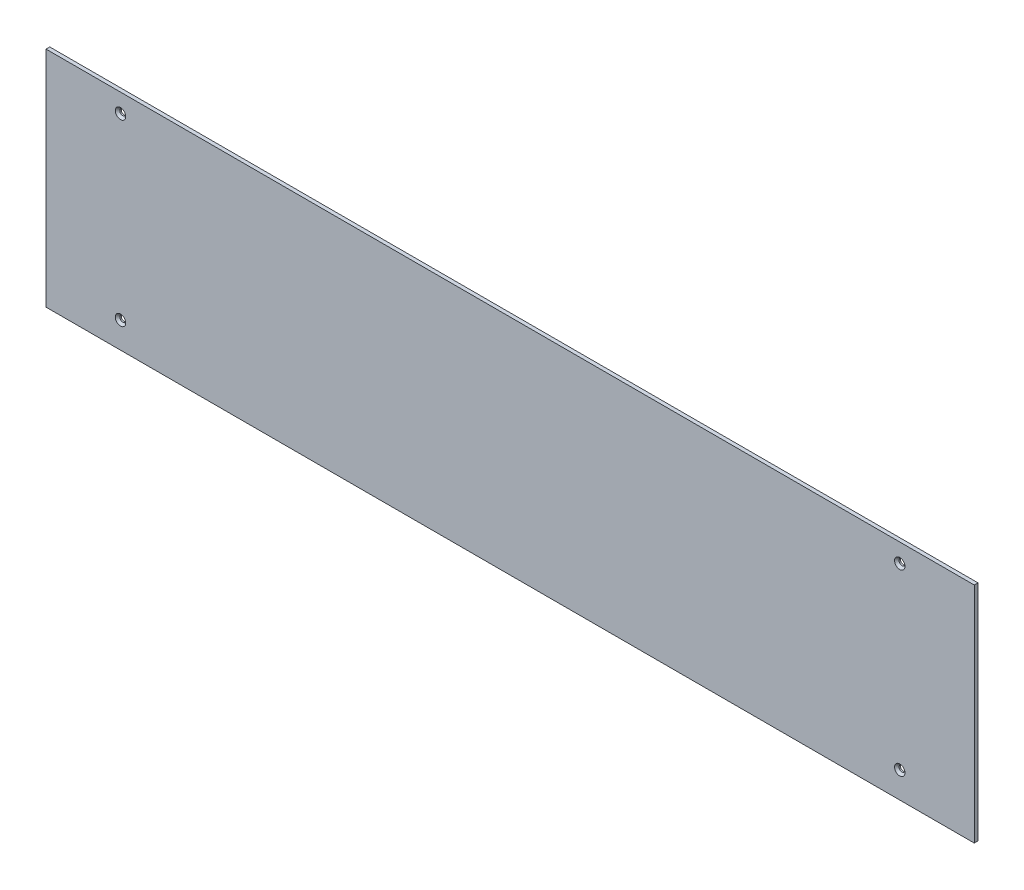
SolidWorks part; units mm, degrees
material "Glass"
ref_plane "Front Plane" through (0, 0, 0) normal (0, 0, 1) x (1, 0, 0)
ref_plane "Top Plane" through (0, 0, 0) normal (0, 1, 0) x (1, 0, 0)
ref_plane "Right Plane" through (0, 0, 0) normal (1, 0, 0) x (0, 0, -1)
sketch "Sketch1" plane through (0, 0, 0) normal (0, 0, 1) x (1, 0, 0)
  line L1 (-623, -150) -> (623, -150)
  line L2 (-623, -150) -> (-623, 150)
  line L3 (-623, 150) -> (623, 150)
  line L4 (623, -150) -> (623, 150)
  line L5 (-623, -150) -> (623, 150) construction
  line L6 (-623, 150) -> (623, -150) construction
  point P0 (0, 0)
  dimension "Largura" = 1246
  dimension "Altura" = 300
extrude "Boss-Extrude1" add sketch "Sketch1" along normal blind 5
sketch "Sketch2" plane through (0, 0, 5) normal (0, 0, 1) x (1, 0, 0)
  line L0 (-623, 150) -> (-623, -150) construction
  line L1 (623, -150) -> (623, 150) construction
  line L2 (623, 150) -> (-623, 150) construction
  line L3 (-623, -150) -> (623, -150) construction
  circle A0 centre (-523, 125) radius 4
  circle A1 centre (523, 125) radius 4
  circle A2 centre (523, -115) radius 4
  circle A3 centre (-523, -115) radius 4
  dimension "D1" = 8
  dimension "D2" = 100
  dimension "D3" = 100
  dimension "D4" = 25
  dimension "D5" = 35
extrude "Cut-Extrude1" cut sketch "Sketch2" against normal through all
chamfer "Chamfer1" distance 3 angle 45 4 edges at (-519, -115, 5) (527, -115, 5) (527, 125, 5) (-519, 125, 5)
